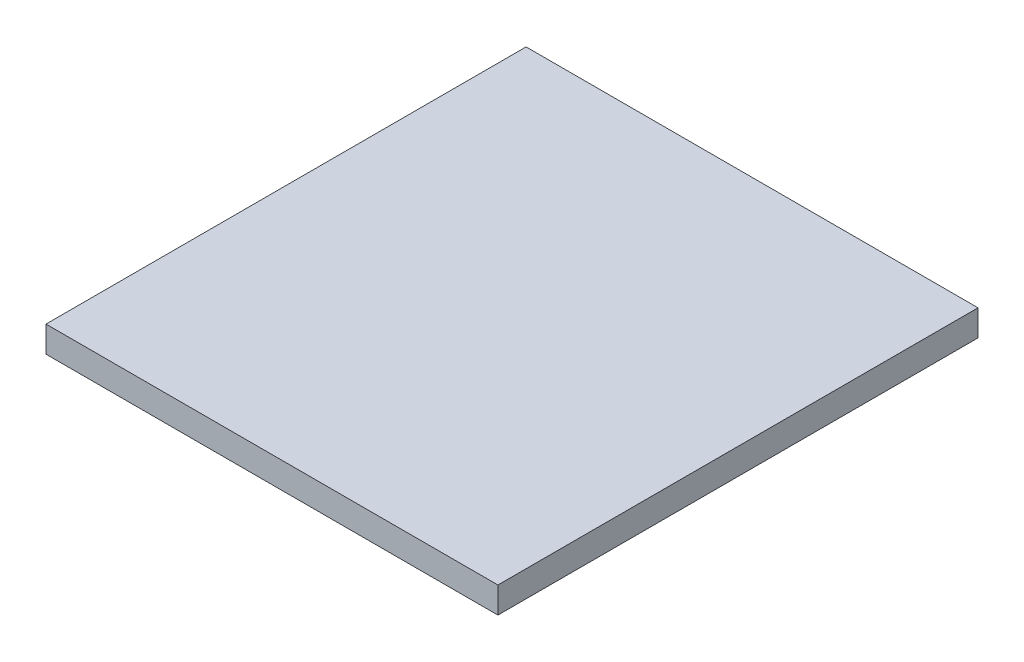
SolidWorks part; units mm, degrees
ref_plane "Front Plane" through (0, 0, 0) normal (0, 0, 1) x (1, 0, 0)
ref_plane "Top Plane" through (0, 0, 0) normal (0, 1, 0) x (1, 0, 0)
ref_plane "Right Plane" through (0, 0, 0) normal (1, 0, 0) x (0, 0, -1)
sketch "Sketch1" plane through (0, 0, 0) normal (0, 1, 0) x (1, 0, 0)
  line L1 (-54.991, -58.42) -> (54.991, -58.42)
  line L2 (-54.991, -58.42) -> (-54.991, 58.42)
  line L3 (-54.991, 58.42) -> (54.991, 58.42)
  line L4 (54.991, -58.42) -> (54.991, 58.42)
  line L5 (-54.991, -58.42) -> (54.991, 58.42) construction
  line L6 (-54.991, 58.42) -> (54.991, -58.42) construction
  point P0 (0, 0)
  dimension "D1" = 109.982
  dimension "D2" = 116.84
extrude "Boss-Extrude1" add sketch "Sketch1" along normal mid plane 6.35
equation "\"material\"=\"GMaterial@Platform.assembly\""
equation "\"D1@Boss-Extrude1\"=\"material\""
